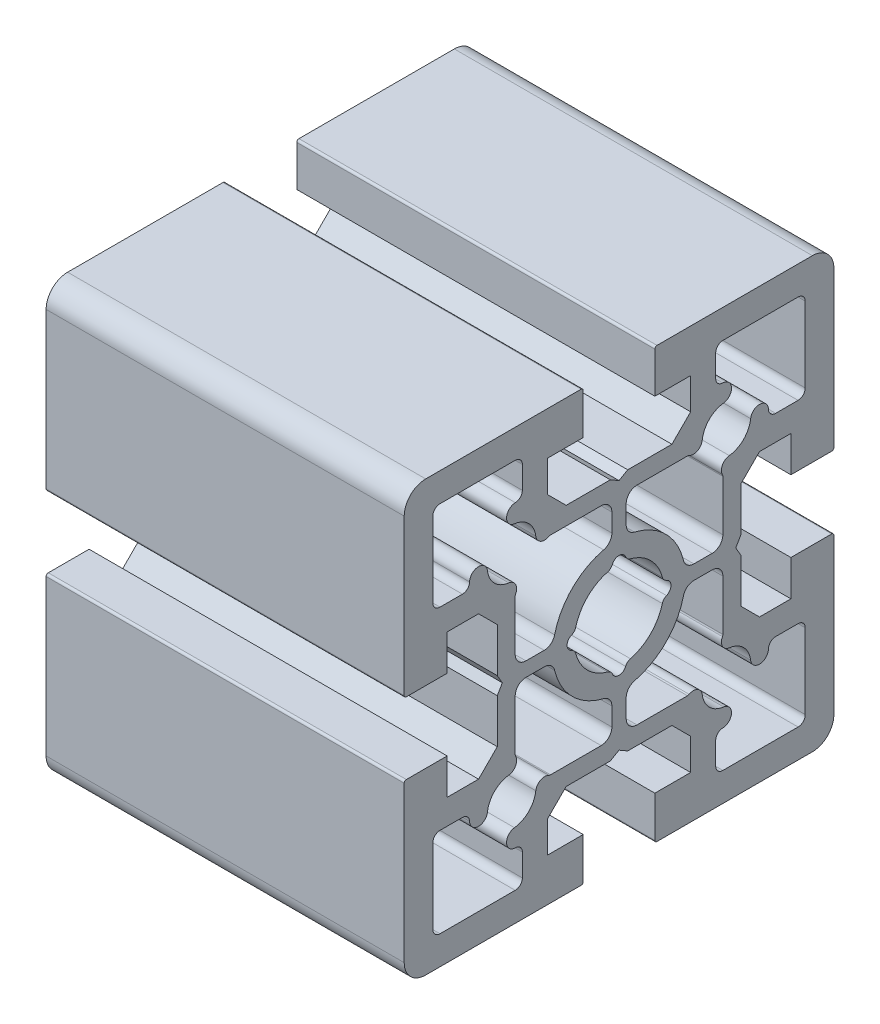
SolidWorks part; units mm, degrees
material "1060 Alloy"
ref_plane "Front Plane" through (0, 0, 0) normal (0, 0, 1) x (1, 0, 0)
ref_plane "Top Plane" through (0, 0, 0) normal (0, 1, 0) x (1, 0, 0)
ref_plane "Right Plane" through (0, 0, 0) normal (1, 0, 0) x (0, 0, -1)
sketch "Sketch1" plane through (0, 0, 0) normal (0, 0, 1) x (1, 0, 0)
  line L0 (-25, 0) -> (25, 0)
  line L1 (0, 0) -> (0, -13.7576) construction
  dimension "D1" = 50
other "Structural Member1"
ref_plane "Plane2" through (-25, 0, 0) normal (1, 0, 0) x (0, 1, 0)
sketch "Sketch12" plane through (-25, 0, 0) normal (1, 0, 0) x (0, 1, 0)
  line L0 (-30, 27) -> (-30, 5.3)
  line L1 (-5.3, 30) -> (-27, 30)
  line L2 (-5, 24) -> (-5, 29.7)
  line L3 (-10, 24) -> (-5, 24)
  line L4 (-10, 19.6167) -> (-10, 24)
  line L5 (-7.3833, 17) -> (-10, 19.6167)
  line L6 (-1.2124, 17) -> (-7.3833, 17)
  line L7 (0, 16.3) -> (-1.2124, 17)
  line L8 (1.2124, 17) -> (0, 16.3)
  line L9 (7.3833, 17) -> (1.2124, 17)
  line L10 (10, 19.6167) -> (7.3833, 17)
  line L11 (10, 24) -> (10, 19.6167)
  line L12 (5, 24) -> (10, 24)
  line L13 (5, 29.7) -> (5, 24)
  line L14 (27, 30) -> (5.3, 30)
  line L15 (30, 5.3) -> (30, 27)
  line L16 (24, 5) -> (29.7, 5)
  line L17 (24, 10) -> (24, 5)
  line L18 (19.6167, 10) -> (24, 10)
  line L19 (17, 7.3833) -> (19.6167, 10)
  line L20 (17, 1.2124) -> (17, 7.3833)
  line L21 (16.3, 0) -> (17, 1.2124)
  line L22 (17, -1.2124) -> (16.3, 0)
  line L23 (17, -7.3833) -> (17, -1.2124)
  line L24 (19.6167, -10) -> (17, -7.3833)
  line L25 (24, -10) -> (19.6167, -10)
  line L26 (24, -5) -> (24, -10)
  line L27 (29.7, -5) -> (24, -5)
  line L28 (30, -27) -> (30, -5.3)
  line L29 (5.3, -30) -> (27, -30)
  line L30 (5, -24) -> (5, -29.7)
  line L31 (10, -24) -> (5, -24)
  line L32 (10, -19.6167) -> (10, -24)
  line L33 (7.3833, -17) -> (10, -19.6167)
  line L34 (1.2124, -17) -> (7.3833, -17)
  line L35 (0, -16.3) -> (1.2124, -17)
  line L36 (-1.2124, -17) -> (0, -16.3)
  line L37 (-7.3833, -17) -> (-1.2124, -17)
  line L38 (-10, -19.6167) -> (-7.3833, -17)
  line L39 (-10, -24) -> (-10, -19.6167)
  line L40 (-5, -24) -> (-10, -24)
  line L41 (-5, -29.7) -> (-5, -24)
  line L42 (-27, -30) -> (-5.3, -30)
  line L43 (-30, -5.3) -> (-30, -27)
  line L44 (-24, -5) -> (-29.7, -5)
  line L45 (-24, -10) -> (-24, -5)
  line L46 (-19.6167, -10) -> (-24, -10)
  line L47 (-17, -7.3833) -> (-19.6167, -10)
  line L48 (-17, -1.2124) -> (-17, -7.3833)
  line L49 (-16.3, 0) -> (-17, -1.2124)
  line L50 (-17, 1.2124) -> (-16.3, 0)
  line L51 (-17, 7.3833) -> (-17, 1.2124)
  line L52 (-19.6167, 10) -> (-17, 7.3833)
  line L53 (-24, 10) -> (-19.6167, 10)
  line L54 (-24, 5) -> (-24, 10)
  line L55 (-29.7, 5) -> (-24, 5)
  line L56 (1, -10.4553) -> (1, -13)
  line L57 (2.5, -14.5) -> (9.5578, -14.5)
  line L58 (13.5, -21.8677) -> (13.5, -25)
  line L59 (14.5, -26) -> (25, -26)
  line L60 (26, -25) -> (26, -14.5)
  line L61 (25, -13.5) -> (21.8677, -13.5)
  line L62 (14.5, -9.5578) -> (14.5, -2.5)
  line L63 (13, -1) -> (10.4553, -1)
  line L64 (1, 13) -> (1, 10.4553)
  line L65 (10.4553, 1) -> (13, 1)
  line L66 (14.5, 2.5) -> (14.5, 9.5578)
  line L67 (21.8677, 13.5) -> (25, 13.5)
  line L68 (26, 14.5) -> (26, 25)
  line L69 (25, 26) -> (14.5, 26)
  line L70 (13.5, 25) -> (13.5, 21.8677)
  line L71 (9.5578, 14.5) -> (2.5, 14.5)
  line L72 (-26, 25) -> (-26, 14.5)
  line L73 (-25, 13.5) -> (-21.8677, 13.5)
  line L74 (-14.5, 9.5578) -> (-14.5, 2.5)
  line L75 (-13, 1) -> (-10.4553, 1)
  line L76 (-1, 10.4553) -> (-1, 13)
  line L77 (-2.5, 14.5) -> (-9.5578, 14.5)
  line L78 (-13.5, 21.8677) -> (-13.5, 25)
  line L79 (-14.5, 26) -> (-25, 26)
  line L80 (-26, -14.5) -> (-26, -25)
  line L81 (-25, -26) -> (-14.5, -26)
  line L82 (-13.5, -25) -> (-13.5, -21.8677)
  line L83 (-9.5578, -14.5) -> (-2.5, -14.5)
  line L84 (-1, -13) -> (-1, -10.4553)
  line L85 (-10.4553, -1) -> (-13, -1)
  line L86 (-14.5, -2.5) -> (-14.5, -9.5578)
  line L87 (-21.8677, -13.5) -> (-25, -13.5)
  line L88 (-30.8485, -27) -> (-23.1515, -27) construction
  line L89 (-27, -30.8485) -> (-27, -23.1515) construction
  line L90 (0.1515, -13) -> (4.8485, -13) construction
  line L91 (2.5, -15.3485) -> (2.5, -10.6515) construction
  line L92 (8.2834, -15.5438) -> (12.4804, -15.5438) construction
  line L93 (10.3819, -17.6423) -> (10.3819, -13.4453) construction
  line L94 (10.7515, -15) -> (19.2485, -15) construction
  line L95 (15, -19.2485) -> (15, -10.7515) construction
  line L96 (12.3577, -19.6181) -> (16.5547, -19.6181) construction
  line L97 (14.4562, -21.7166) -> (14.4562, -17.5196) construction
  line L98 (23.1515, -14.5) -> (26.8485, -14.5) construction
  line L99 (25, -16.3485) -> (25, -12.6515) construction
  line L100 (17.5196, -14.4562) -> (21.7166, -14.4562) construction
  line L101 (19.6181, -16.5547) -> (19.6181, -12.3577) construction
  line L102 (13.4453, -10.3819) -> (17.6423, -10.3819) construction
  line L103 (15.5438, -12.4804) -> (15.5438, -8.2834) construction
  line L104 (10.6515, -2.5) -> (15.3485, -2.5) construction
  line L105 (13, -4.8485) -> (13, -0.1515) construction
  line L106 (-10.0985, 0) -> (10.0985, 0) construction
  line L107 (0, -10.0985) -> (0, 10.0985) construction
  line L108 (10.6515, 2.5) -> (15.3485, 2.5) construction
  line L109 (13, 0.1515) -> (13, 4.8485) construction
  line L110 (13.4453, 10.3819) -> (17.6423, 10.3819) construction
  line L111 (15.5438, 8.2834) -> (15.5438, 12.4804) construction
  line L112 (10.7515, 15) -> (19.2485, 15) construction
  line L113 (15, 10.7515) -> (15, 19.2485) construction
  line L114 (17.5196, 14.4562) -> (21.7166, 14.4562) construction
  line L115 (19.6181, 12.3577) -> (19.6181, 16.5547) construction
  line L116 (12.6515, 25) -> (16.3485, 25) construction
  line L117 (14.5, 23.1515) -> (14.5, 26.8485) construction
  line L118 (12.3577, 19.6181) -> (16.5547, 19.6181) construction
  line L119 (14.4562, 17.5196) -> (14.4562, 21.7166) construction
  line L120 (8.2834, 15.5438) -> (12.4804, 15.5438) construction
  line L121 (10.3819, 13.4453) -> (10.3819, 17.6423) construction
  line L122 (-6.25, -1.8485) -> (-6.25, 1.8485) construction
  line L123 (-1.8485, -6.25) -> (1.8485, -6.25) construction
  line L124 (6.25, -1.8485) -> (6.25, 1.8485) construction
  line L125 (-1.8485, 6.25) -> (1.8485, 6.25) construction
  line L126 (-21.7166, 14.4562) -> (-17.5196, 14.4562) construction
  line L127 (-19.6181, 12.3577) -> (-19.6181, 16.5547) construction
  line L128 (-19.2485, 15) -> (-10.7515, 15) construction
  line L129 (-15, 10.7515) -> (-15, 19.2485) construction
  line L130 (-17.6423, 10.3819) -> (-13.4453, 10.3819) construction
  line L131 (-15.5438, 8.2834) -> (-15.5438, 12.4804) construction
  line L132 (-15.3485, 2.5) -> (-10.6515, 2.5) construction
  line L133 (-13, 0.1515) -> (-13, 4.8485) construction
  line L134 (-12.4804, 15.5438) -> (-8.2834, 15.5438) construction
  line L135 (-10.3819, 13.4453) -> (-10.3819, 17.6423) construction
  line L136 (-16.5547, 19.6181) -> (-12.3577, 19.6181) construction
  line L137 (-14.4562, 17.5196) -> (-14.4562, 21.7166) construction
  line L138 (-16.3485, -25) -> (-12.6515, -25) construction
  line L139 (-14.5, -26.8485) -> (-14.5, -23.1515) construction
  line L140 (-16.5547, -19.6181) -> (-12.3577, -19.6181) construction
  line L141 (-14.4562, -21.7166) -> (-14.4562, -17.5196) construction
  line L142 (-19.2485, -15) -> (-10.7515, -15) construction
  line L143 (-15, -19.2485) -> (-15, -10.7515) construction
  line L144 (-12.4804, -15.5438) -> (-8.2834, -15.5438) construction
  line L145 (-10.3819, -17.6423) -> (-10.3819, -13.4453) construction
  line L146 (-15.3485, -2.5) -> (-10.6515, -2.5) construction
  line L147 (-13, -4.8485) -> (-13, -0.1515) construction
  line L148 (-17.6423, -10.3819) -> (-13.4453, -10.3819) construction
  line L149 (-15.5438, -12.4804) -> (-15.5438, -8.2834) construction
  line L150 (-21.7166, -14.4562) -> (-17.5196, -14.4562) construction
  line L151 (-19.6181, -16.5547) -> (-19.6181, -12.3577) construction
  arc A0 (-27, 30) -> (-30, 27) centre (-27, 27) ccw
  arc A1 (-5, 29.7) -> (-5.3, 30) centre (-5.3, 29.7) ccw
  arc A2 (5.3, 30) -> (5, 29.7) centre (5.3, 29.7) ccw
  arc A3 (30, 27) -> (27, 30) centre (27, 27) ccw
  arc A4 (29.7, 5) -> (30, 5.3) centre (29.7, 5.3) ccw
  arc A5 (30, -5.3) -> (29.7, -5) centre (29.7, -5.3) ccw
  arc A6 (27, -30) -> (30, -27) centre (27, -27) ccw
  arc A7 (5, -29.7) -> (5.3, -30) centre (5.3, -29.7) ccw
  arc A8 (-5.3, -30) -> (-5, -29.7) centre (-5.3, -29.7) ccw
  arc A9 (-30, -27) -> (-27, -30) centre (-27, -27) ccw
  arc A10 (-29.7, -5) -> (-30, -5.3) centre (-29.7, -5.3) ccw
  arc A11 (-30, 5.3) -> (-29.7, 5) centre (-29.7, 5.3) ccw
  arc A12 (1, -13) -> (2.5, -14.5) centre (2.5, -13) ccw
  arc A13 (9.5578, -14.5) -> (9.7932, -14.4411) centre (9.5578, -14) ccw
  arc A14 (11.6233, -15.3976) -> (9.7932, -14.4411) centre (10.3819, -15.5438) ccw
  arc A15 (11.6233, -15.3976) -> (14.6024, -18.3767) centre (15, -15) ccw
  arc A16 (14.4805, -20.8679) -> (14.6024, -18.3767) centre (14.4562, -19.6181) ccw
  arc A17 (14.4805, -20.8679) -> (13.5, -21.8677) centre (14.5, -21.8677) ccw
  arc A18 (13.5, -25) -> (14.5, -26) centre (14.5, -25) ccw
  arc A19 (25, -26) -> (26, -25) centre (25, -25) ccw
  arc A20 (26, -14.5) -> (25, -13.5) centre (25, -14.5) ccw
  arc A21 (21.8677, -13.5) -> (20.8679, -14.4805) centre (21.8677, -14.5) ccw
  arc A22 (18.3767, -14.6024) -> (20.8679, -14.4805) centre (19.6181, -14.4562) ccw
  arc A23 (18.3767, -14.6024) -> (15.3976, -11.6233) centre (15, -15) ccw
  arc A24 (14.4411, -9.7932) -> (15.3976, -11.6233) centre (15.5438, -10.3819) ccw
  arc A25 (14.4411, -9.7932) -> (14.5, -9.5578) centre (14, -9.5578) ccw
  arc A26 (14.5, -2.5) -> (13, -1) centre (13, -2.5) ccw
  arc A27 (10.4553, -1) -> (8.9964, -2.1512) centre (10.4553, -2.5) ccw
  arc A28 (2.1512, -8.9964) -> (8.9964, -2.1512) centre (0, 0) ccw
  arc A29 (2.1512, -8.9964) -> (1, -10.4553) centre (2.5, -10.4553) ccw
  arc A30 (2.5, 14.5) -> (1, 13) centre (2.5, 13) ccw
  arc A31 (1, 10.4553) -> (2.1512, 8.9964) centre (2.5, 10.4553) ccw
  arc A32 (8.9964, 2.1512) -> (2.1512, 8.9964) centre (0, 0) ccw
  arc A33 (8.9964, 2.1512) -> (10.4553, 1) centre (10.4553, 2.5) ccw
  arc A34 (13, 1) -> (14.5, 2.5) centre (13, 2.5) ccw
  arc A35 (14.5, 9.5578) -> (14.4411, 9.7932) centre (14, 9.5578) ccw
  arc A36 (15.3976, 11.6233) -> (14.4411, 9.7932) centre (15.5438, 10.3819) ccw
  arc A37 (15.3976, 11.6233) -> (18.3767, 14.6024) centre (15, 15) ccw
  arc A38 (20.8679, 14.4805) -> (18.3767, 14.6024) centre (19.6181, 14.4562) ccw
  arc A39 (20.8679, 14.4805) -> (21.8677, 13.5) centre (21.8677, 14.5) ccw
  arc A40 (25, 13.5) -> (26, 14.5) centre (25, 14.5) ccw
  arc A41 (26, 25) -> (25, 26) centre (25, 25) ccw
  arc A42 (14.5, 26) -> (13.5, 25) centre (14.5, 25) ccw
  arc A43 (13.5, 21.8677) -> (14.4805, 20.8679) centre (14.5, 21.8677) ccw
  arc A44 (14.6024, 18.3767) -> (14.4805, 20.8679) centre (14.4562, 19.6181) ccw
  arc A45 (14.6024, 18.3767) -> (11.6233, 15.3976) centre (15, 15) ccw
  arc A46 (9.7932, 14.4411) -> (11.6233, 15.3976) centre (10.3819, 15.5438) ccw
  arc A47 (9.7932, 14.4411) -> (9.5578, 14.5) centre (9.5578, 14) ccw
  arc A48 (-6.63, 0.925) -> (-6.0431, 1.5948) centre (-7.01, 1.85) ccw
  arc A49 (-6.63, 0.925) -> (-6.63, -0.925) centre (-6.25, 0) ccw
  arc A50 (-6.0431, -1.5948) -> (-6.63, -0.925) centre (-7.01, -1.85) ccw
  arc A51 (-6.0431, -1.5948) -> (-1.5948, -6.0431) centre (0, 0) ccw
  arc A52 (-0.925, -6.63) -> (-1.5948, -6.0431) centre (-1.85, -7.01) ccw
  arc A53 (-0.925, -6.63) -> (0.925, -6.63) centre (0, -6.25) ccw
  arc A54 (1.5948, -6.0431) -> (0.925, -6.63) centre (1.85, -7.01) ccw
  arc A55 (1.5948, -6.0431) -> (6.0431, -1.5948) centre (0, 0) ccw
  arc A56 (6.63, -0.925) -> (6.0431, -1.5948) centre (7.01, -1.85) ccw
  arc A57 (6.63, -0.925) -> (6.63, 0.925) centre (6.25, 0) ccw
  arc A58 (6.0431, 1.5948) -> (6.63, 0.925) centre (7.01, 1.85) ccw
  arc A59 (6.0431, 1.5948) -> (1.5949, 6.043) centre (0.0001, 0.0001) ccw
  arc A60 (0.9249, 6.6302) -> (1.5949, 6.043) centre (1.8499, 7.0099) ccw
  arc A61 (0.9249, 6.6302) -> (-0.925, 6.63) centre (0, 6.25) ccw
  arc A62 (-1.5948, 6.0431) -> (-0.925, 6.63) centre (-1.85, 7.01) ccw
  arc A63 (-1.5948, 6.0431) -> (-6.0431, 1.5948) centre (0, 0) ccw
  arc A64 (-25, 26) -> (-26, 25) centre (-25, 25) ccw
  arc A65 (-26, 14.5) -> (-25, 13.5) centre (-25, 14.5) ccw
  arc A66 (-21.8677, 13.5) -> (-20.8679, 14.4805) centre (-21.8677, 14.5) ccw
  arc A67 (-18.3767, 14.6024) -> (-20.8679, 14.4805) centre (-19.6181, 14.4562) ccw
  arc A68 (-18.3767, 14.6024) -> (-15.3976, 11.6233) centre (-15, 15) ccw
  arc A69 (-14.4411, 9.7932) -> (-15.3976, 11.6233) centre (-15.5438, 10.3819) ccw
  arc A70 (-14.4411, 9.7932) -> (-14.5, 9.5578) centre (-14, 9.5578) ccw
  arc A71 (-14.5, 2.5) -> (-13, 1) centre (-13, 2.5) ccw
  arc A72 (-10.4553, 1) -> (-8.9964, 2.1512) centre (-10.4553, 2.5) ccw
  arc A73 (-2.1512, 8.9964) -> (-8.9964, 2.1512) centre (0, 0) ccw
  arc A74 (-2.1512, 8.9964) -> (-1, 10.4553) centre (-2.5, 10.4553) ccw
  arc A75 (-1, 13) -> (-2.5, 14.5) centre (-2.5, 13) ccw
  arc A76 (-9.5578, 14.5) -> (-9.7932, 14.4411) centre (-9.5578, 14) ccw
  arc A77 (-11.6233, 15.3976) -> (-9.7932, 14.4411) centre (-10.3819, 15.5438) ccw
  arc A78 (-11.6233, 15.3976) -> (-14.6024, 18.3767) centre (-15, 15) ccw
  arc A79 (-14.4805, 20.8679) -> (-14.6024, 18.3767) centre (-14.4562, 19.6181) ccw
  arc A80 (-14.4805, 20.8679) -> (-13.5, 21.8677) centre (-14.5, 21.8677) ccw
  arc A81 (-13.5, 25) -> (-14.5, 26) centre (-14.5, 25) ccw
  arc A82 (-26, -25) -> (-25, -26) centre (-25, -25) ccw
  arc A83 (-14.5, -26) -> (-13.5, -25) centre (-14.5, -25) ccw
  arc A84 (-13.5, -21.8677) -> (-14.4805, -20.8679) centre (-14.5, -21.8677) ccw
  arc A85 (-14.6024, -18.3767) -> (-14.4805, -20.8679) centre (-14.4562, -19.6181) ccw
  arc A86 (-14.6024, -18.3767) -> (-11.6233, -15.3976) centre (-15, -15) ccw
  arc A87 (-9.7932, -14.4411) -> (-11.6233, -15.3976) centre (-10.3819, -15.5438) ccw
  arc A88 (-9.7932, -14.4411) -> (-9.5578, -14.5) centre (-9.5578, -14) ccw
  arc A89 (-2.5, -14.5) -> (-1, -13) centre (-2.5, -13) ccw
  arc A90 (-1, -10.4553) -> (-2.1512, -8.9964) centre (-2.5, -10.4553) ccw
  arc A91 (-8.9964, -2.1512) -> (-2.1512, -8.9964) centre (0, 0) ccw
  arc A92 (-8.9964, -2.1512) -> (-10.4553, -1) centre (-10.4553, -2.5) ccw
  arc A93 (-13, -1) -> (-14.5, -2.5) centre (-13, -2.5) ccw
  arc A94 (-14.5, -9.5578) -> (-14.4411, -9.7932) centre (-14, -9.5578) ccw
  arc A95 (-15.3976, -11.6233) -> (-14.4411, -9.7932) centre (-15.5438, -10.3819) ccw
  arc A96 (-15.3976, -11.6233) -> (-18.3767, -14.6024) centre (-15, -15) ccw
  arc A97 (-20.8679, -14.4805) -> (-18.3767, -14.6024) centre (-19.6181, -14.4562) ccw
  arc A98 (-20.8679, -14.4805) -> (-21.8677, -13.5) centre (-21.8677, -14.5) ccw
  arc A99 (-25, -13.5) -> (-26, -14.5) centre (-25, -14.5) ccw
  point P0 (0, 0)
